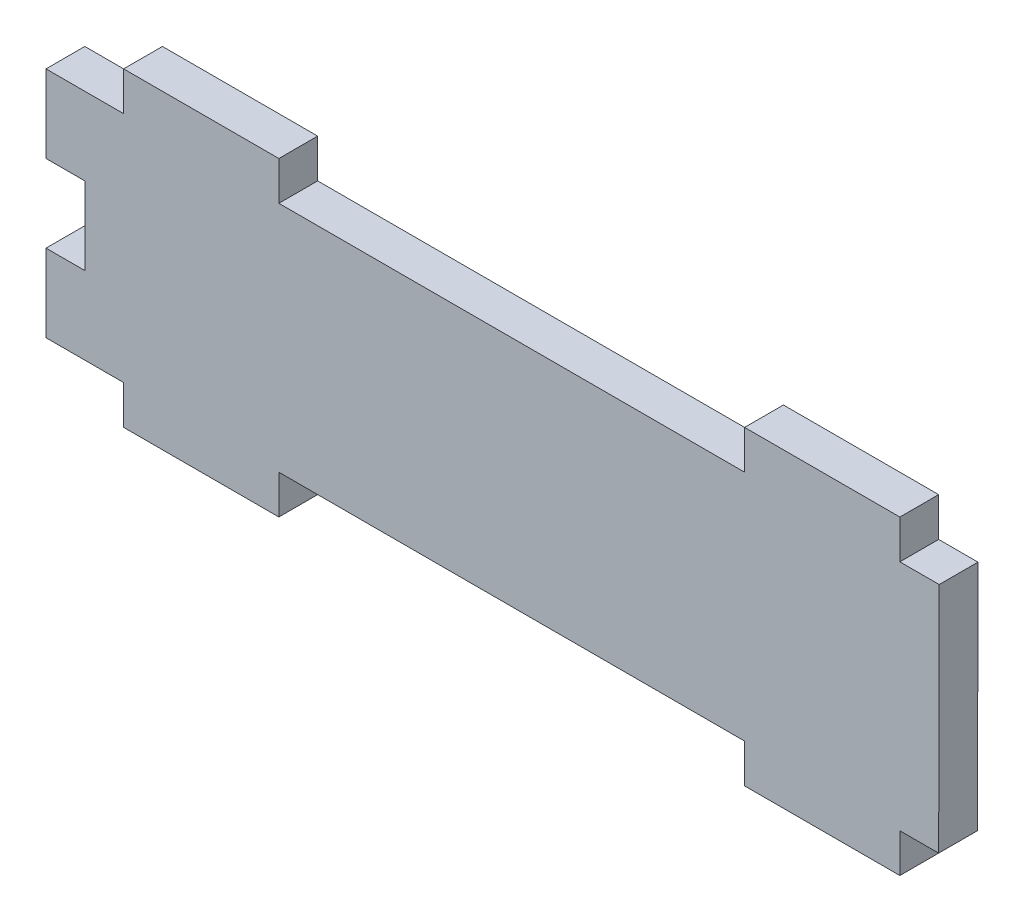
SolidWorks part; units mm, degrees
ref_plane "Front Plane" through (0, 0, 0) normal (0, 0, 1) x (1, 0, 0)
ref_plane "Top Plane" through (0, 0, 0) normal (0, 1, 0) x (1, 0, 0)
ref_plane "Right Plane" through (0, 0, 0) normal (1, 0, 0) x (0, 0, -1)
sketch "Sketch1" plane through (0, 0, 0) normal (0, 0, 1) x (1, 0, 0)
  line L0 (0, 44.45) -> (6.35, 44.45)
  line L1 (6.35, 6.35) -> (12.7, 6.35)
  line L2 (0, 44.45) -> (0, 31.75)
  line L3 (6.35, 44.45) -> (12.7, 44.45)
  line L4 (139.7005, 44.4499) -> (146.1347, 44.4499)
  line L5 (12.7, 50.8) -> (38.1, 50.8)
  line L6 (6.35, 31.75) -> (6.35, 19.05)
  line L7 (12.7, 0) -> (38.1, 0)
  line L8 (146.1347, 44.4499) -> (146.05, 6.35)
  line L9 (0, 6.35) -> (6.35, 6.35)
  line L10 (0, 31.75) -> (6.35, 31.75)
  line L11 (0, 19.05) -> (6.35, 19.05)
  line L12 (0, 19.05) -> (0, 6.35)
  line L13 (139.7, 6.35) -> (146.05, 6.35)
  line L18 (12.7, 44.45) -> (12.7, 50.8)
  line L19 (38.1, 44.45) -> (38.1, 50.8)
  line L20 (12.7, 6.35) -> (12.7, 0)
  line L21 (38.1, 6.35) -> (38.1, 0)
  line L22 (139.7005, 44.4499) -> (139.7005, 50.8)
  line L23 (114.3, 44.45) -> (114.3, 50.8)
  line L24 (114.3, 6.35) -> (114.3, 0)
  line L25 (139.7, 6.35) -> (139.7, 0)
  line L26 (38.1, 44.45) -> (114.3, 44.45)
  line L27 (114.3, 50.8) -> (139.7005, 50.8)
  line L29 (38.1, 6.35) -> (114.3, 6.35)
  line L30 (114.3, 0) -> (139.7, 0)
extrude "Boss-Extrude1" add sketch "Sketch1" along normal blind 6.35
sketch "Sketch2" plane through (0, 0, 6.35) normal (0, 0, 1) x (1, 0, 0)
